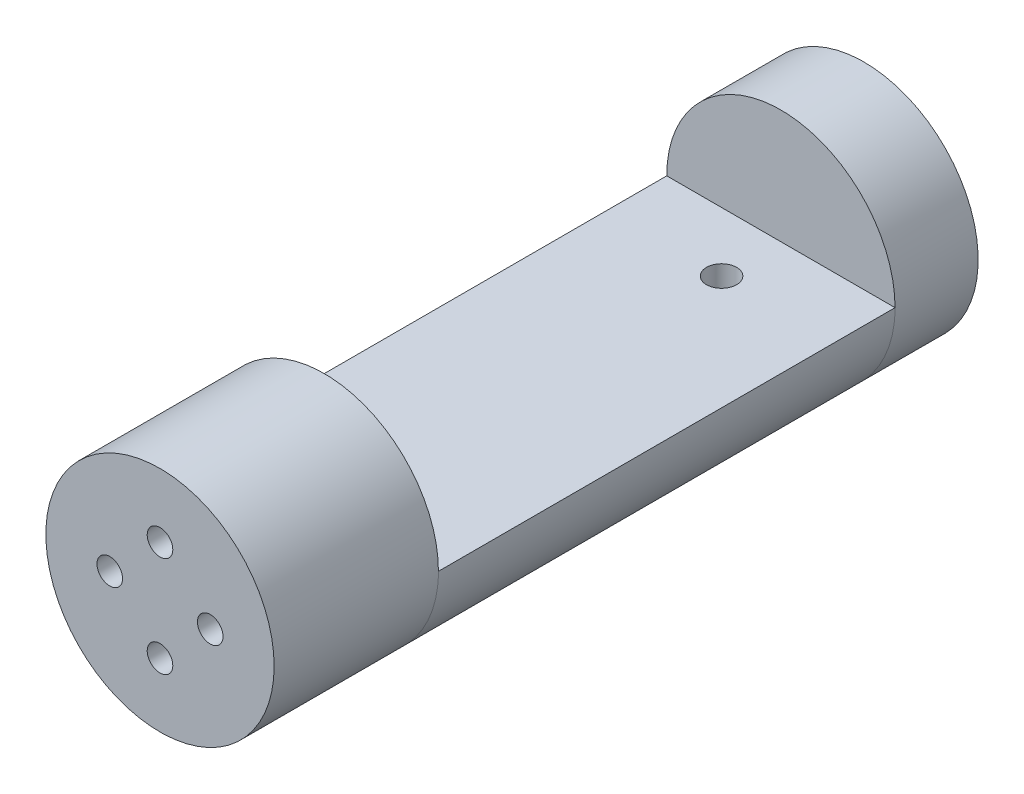
SolidWorks part; units mm, degrees
ref_plane "Front Plane" through (0, 0, 0) normal (0, 0, 1) x (1, 0, 0)
ref_plane "Top Plane" through (0, 0, 0) normal (0, 1, 0) x (1, 0, 0)
ref_plane "Right Plane" through (0, 0, 0) normal (1, 0, 0) x (0, 0, -1)
sketch "Sketch1" plane through (0, 0, 0) normal (0, 0, 1) x (1, 0, 0)
  circle A0 centre (0, 0) radius 12.5
  point P3 (0, 0)
  dimension "D1" = 25
extrude "Boss-Extrude1" add sketch "Sketch1" along normal blind 17.99
sketch "Sketch2" plane through (0, 0, 17.99) normal (0, 0, 1) x (1, 0, 0)
  circle A0 centre (0, 0) radius 5.5
  circle A1 centre (0, -5.5) radius 1.4
  circle A2 centre (-5.5, 0) radius 1.4
  circle A3 centre (0, 5.5) radius 1.4
  circle A4 centre (5.5, 0) radius 1.4
  dimension "D1" = 11
  dimension "D2" = 2.8
  dimension "D3" = 2.8
  dimension "D4" = 2.8
  dimension "D5" = 2.8
extrude "Cut-Extrude1" cut sketch "Sketch2" against normal blind 8 contours A2 | A3 | A4 | A1
sketch "Sketch3" plane through (0, 0, 0) normal (0, 0, -1) x (-1, 0, 0)
  point P3 (0, 0)
  point P5 (0, 0)
  point P6 (0, 8.5096)
  point P7 (-0.8851, 8.5005)
  point P8 (0, 8.5807)
  point P9 (0, 0)
sketch "Sketch4" plane through (0, 0, 0) normal (0, 0, -1) x (-1, 0, 0)
  line L0 (-12.5, 0) -> (12.5, 0)
  circle A0 centre (0, 0) radius 12.5 construction
  ellipse E0 centre (0, 0) end of major axis (0, 12.5) minor radius 12.5 (12.5, 0) -> (-12.5, 0) cw
  point P7 (0, 0)
extrude "Boss-Extrude3" add sketch "Sketch4" along normal blind 50 contours L0 E0
sketch "Sketch6" plane through (0, 0, -50) normal (0, 0, -1) x (-1, 0, 0)
  line L0 (-12.5, 0) -> (12.5, 0) construction
  circle A0 centre (0, 0) radius 12.5
extrude "Boss-Extrude4" add sketch "Sketch6" along normal blind 9.1
sketch "Sketch7" plane through (0, 0, 0) normal (0, 1, 0) x (1, 0, 0)
  line L0 (0, 50) -> (0, 0) construction
  line L1 (12.5, 50) -> (-12.5, 50) construction
  circle A0 centre (0, 43.5) radius 1.65
  circle A1 centre (0, 6.5) radius 1.65
  point P8 (0, 25)
  dimension "D2" = 3.3
  dimension "D3" = 3.3
  dimension "D1" = 37
extrude "Cut-Extrude2" cut sketch "Sketch7" against normal blind 10
